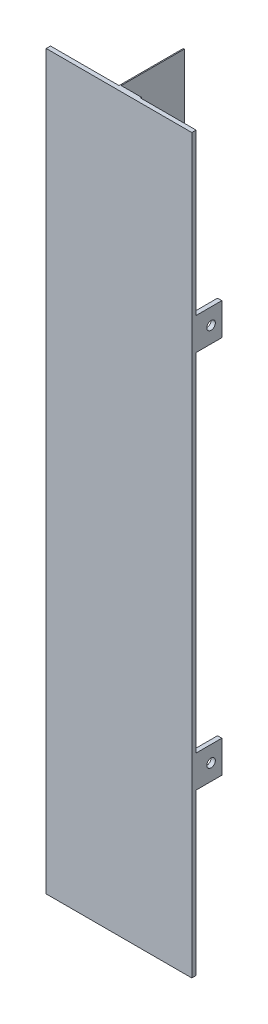
SolidWorks part; units mm, degrees
material "PPS"
ref_plane "Płaszczyzna XY" through (0, 0, 0) normal (0, 0, 1) x (1, 0, 0)
ref_plane "Płaszczyzna XZ" through (0, 0, 0) normal (0, 1, 0) x (1, 0, 0)
ref_plane "Płaszczyzna YZ" through (0, 0, 0) normal (1, 0, 0) x (0, 0, -1)
sketch "Szkic1" plane through (0, 0, 0) normal (0, 1, 0) x (1, 0, 0)
  line L0 (0, 0) -> (0, 2)
  line L1 (0, 2) -> (32, 2)
  line L2 (32, 2) -> (32, 32)
  line L3 (32, 32) -> (32.5, 32)
  line L4 (32.5, 32) -> (32.5, 2.5)
  line L5 (32.5, 2.5) -> (42, 2.5)
  line L6 (42, 2.5) -> (42, 2)
  line L7 (42, 2) -> (68, 2)
  line L8 (68, 2) -> (68, 0)
  line L9 (68, 0) -> (0, 0)
  dimension "D1" = 2
  dimension "D2" = 0.5
  dimension "D3" = 2
  dimension "D4" = 68
  dimension "D5" = 0.5
  dimension "D6" = 26
  dimension "D7" = 32
  dimension "D8" = 30
extrude "Dodanie-wyciągnięcie1" add sketch "Szkic1" along normal blind 342
sketch "Szkic3" plane through (0, 0, -2) normal (0, 0, -1) x (-1, 0, 0)
  line L0 (-68, 342) -> (-68, 0) construction
  line L1 (-68, 75) -> (-66, 75)
  line L2 (-68, 75) -> (-68, 90)
  line L3 (-68, 90) -> (-66, 90)
  line L4 (-66, 75) -> (-66, 90)
  line L5 (0, 342) -> (0, 0) construction
  line L10 (-68, 252) -> (-66, 252)
  line L11 (-68, 252) -> (-68, 267)
  line L12 (-68, 267) -> (-66, 267)
  line L13 (-66, 252) -> (-66, 267)
  line L14 (0, 75) -> (-2, 75)
  line L15 (0, 75) -> (0, 90)
  line L16 (0, 90) -> (-2, 90)
  line L17 (-2, 75) -> (-2, 90)
  line L18 (-32, 0) -> (0, 0) construction
  line L23 (0, 252) -> (-2, 252)
  line L24 (0, 252) -> (0, 267)
  line L25 (0, 267) -> (-2, 267)
  line L26 (-2, 252) -> (-2, 267)
  line L27 (-68, 0) -> (-42, 0) construction
  line L28 (-68, 342) -> (-42, 342) construction
  line L29 (-32, 342) -> (0, 342) construction
  dimension "D1" = 15
  dimension "D3" = 15
  dimension "D4" = 15
  dimension "D6" = 15
  dimension "D7" = 2
  dimension "D9" = 2
  dimension "D10" = 2
  dimension "D12" = 2
  dimension "D13" = 75
  dimension "D14" = 75
  dimension "D15" = 75
  dimension "D16" = 75
extrude "Dodanie-wyciągnięcie2" add sketch "Szkic3" along normal blind 12
sketch "Szkic4" plane through (0, 0, 0) normal (-1, 0, 0) x (0, 0, 1)
  line L0 (-14, 90) -> (-2, 90) construction
  line L1 (-14, 75) -> (-14, 90) construction
  line L2 (-14, 267) -> (-2, 267) construction
  line L3 (-14, 252) -> (-14, 267) construction
  circle A0 centre (-9, 82.5) radius 2
  circle A1 centre (-9, 259.5) radius 2
  dimension "D1" = 7.5
  dimension "D2" = 5
  dimension "D3" = 4
  dimension "D4" = 7.5
  dimension "D5" = 5
  dimension "D6" = 4
sketch "Szkic5" plane through (68, 0, 0) normal (1, 0, 0) x (0, 0, -1)
  circle A0 centre (9, 259.5) radius 2
  circle A1 centre (9, 82.5) radius 2
  dimension "D1" = 4
  dimension "D2" = 4
extrude "Wytnij-wyciągnięcie1" cut sketch "Szkic4" against normal blind 10
extrude "Wytnij-wyciągnięcie2" cut sketch "Szkic5" against normal blind 10
